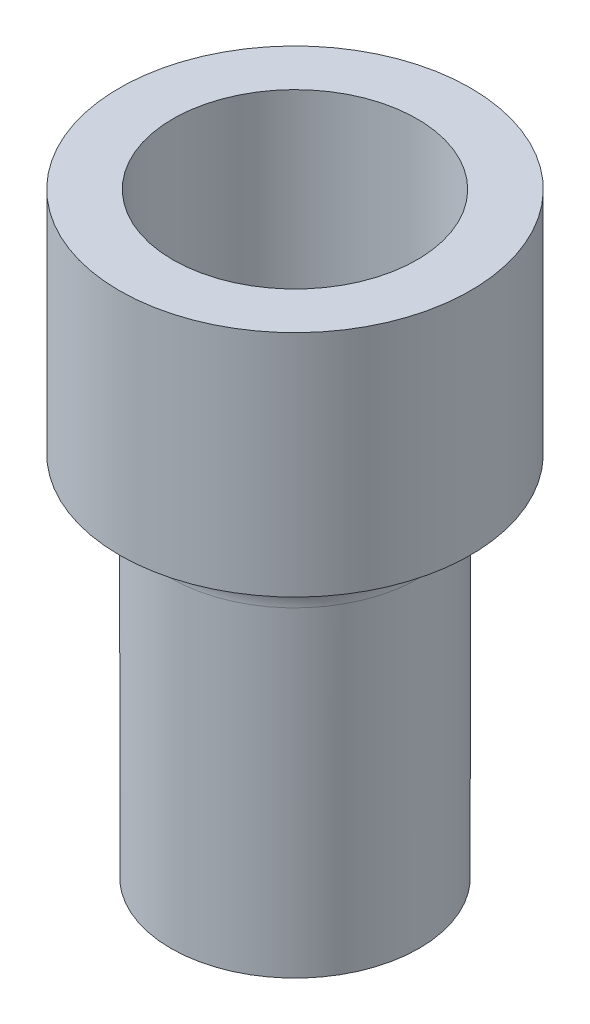
SolidWorks part; units mm, degrees
ref_plane "Front Plane" through (0, 0, 0) normal (0, 0, 1) x (1, 0, 0)
ref_plane "Top Plane" through (0, 0, 0) normal (0, 1, 0) x (1, 0, 0)
ref_plane "Right Plane" through (0, 0, 0) normal (1, 0, 0) x (0, 0, -1)
sketch "Sketch1" plane through (0, 0, 0) normal (0, 1, 0) x (1, 0, 0)
  circle A0 centre (0, 0) radius 4.064
  circle A1 centre (0, 0) radius 5.842
  dimension "D1" = 8.128
  dimension "D2" = 1.778
extrude "Boss-Extrude1" add sketch "Sketch1" along normal blind 7.62
sketch "Sketch3" plane through (0, 0, 0) normal (0, -1, 0) x (1, 0, 0)
  circle A0 centre (0, 0) radius 4.1275
  dimension "D1" = 8.255
extrude "Boss-Extrude2" add sketch "Sketch3" along normal blind 12.192
fillet "Fillet2" radius 1.524 1 edges at (0, 0, 4.1275)
